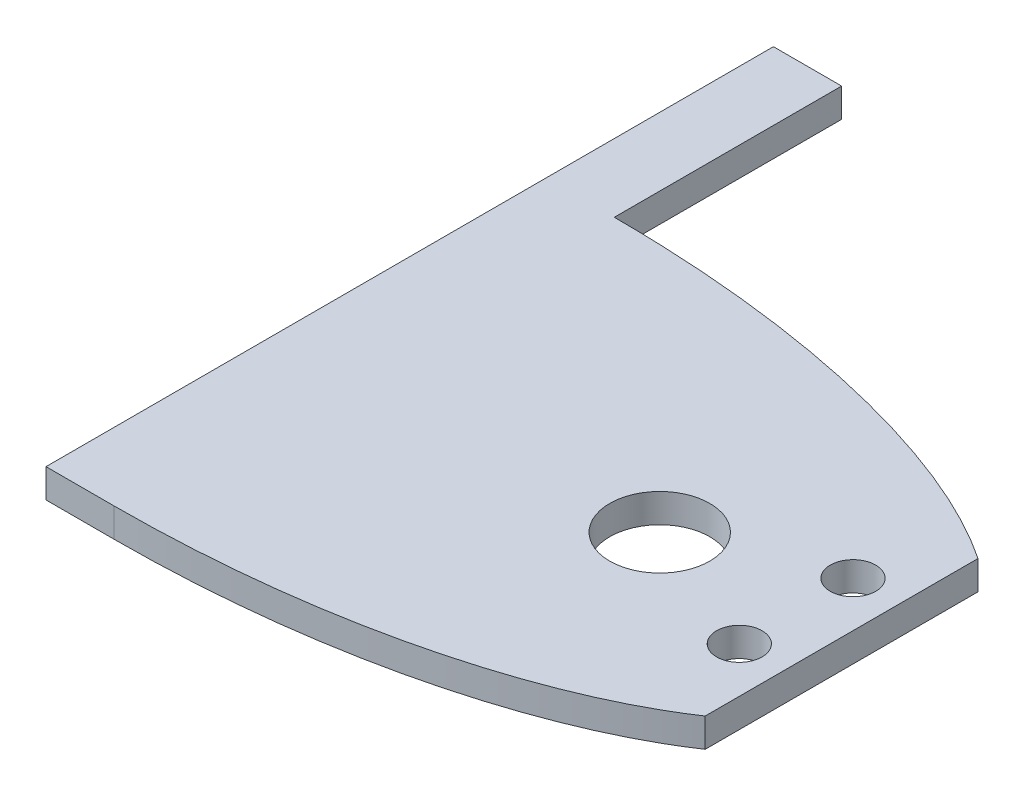
SolidWorks part; units mm, degrees
ref_plane "Front Plane" through (0, 0, 0) normal (0, 0, 1) x (1, 0, 0)
ref_plane "Top Plane" through (0, 0, 0) normal (0, 1, 0) x (1, 0, 0)
ref_plane "Right Plane" through (0, 0, 0) normal (1, 0, 0) x (0, 0, -1)
sketch "Sketch1" plane through (0, 0, 0) normal (0, 1, 0) x (1, 0, 0)
  line L1 (0, 110) -> (0, 0)
  line L2 (105, 85) -> (105, 25)
  ellipse E0 centre (0, 55) end of major axis (-125.2773, 55) minor radius 55 (105, 85) -> (0, 110) ccw
  ellipse E1 centre (0, 55) end of major axis (-125.2773, 55) minor radius 55 (0, 0) -> (105, 25) ccw
  dimension "D1" = 110
  dimension "D2" = 60
  dimension "D3" = 105
extrude "Boss-Extrude1" add sketch "Sketch1" along normal blind 6.35
sketch "Sketch2" plane through (0, 0, 0) normal (0, 1, 0) x (1, 0, 0)
  circle A0 centre (95, 67.5) radius 5
  circle A1 centre (95, 42.5) radius 5
  dimension "D1" = 10
  dimension "D4" = 10
  dimension "D2" = 17.5
  dimension "D3" = 42.5
extrude "Cut-Extrude1" cut sketch "Sketch2" along normal blind 6.35
sketch "Sketch3" plane through (0, 0, 0) normal (0, 1, 0) x (1, 0, 0)
  circle A0 centre (65, 55) radius 11
  dimension "D2" = 22
  dimension "D1" = 30
  dimension "D3" = 40
extrude "Cut-Extrude2" cut sketch "Sketch3" along normal through all
sketch "Sketch4" plane through (0, 0, 0) normal (0, 1, 0) x (1, 0, 0)
  line L0 (0, 110) -> (-15, 110)
  line L1 (0, 110) -> (0, 0) construction
  line L2 (-15, 110) -> (-15, 0)
  line L3 (-15, 0) -> (0, 0)
  line L4 (0, 0) -> (0, 110)
  ellipse E0 centre (0, 55) end of major axis (-125.2773, 55) minor radius 55 (105, 85) -> (0, 110) ccw construction
  dimension "D1" = 15
extrude "Boss-Extrude3" add sketch "Sketch4" along normal blind 6.35
sketch "Sketch5" plane through (0, 0, 0) normal (0, 1, 0) x (1, 0, 0)
  line L0 (-15, 110) -> (-15, 160)
  line L1 (-15, 160) -> (0, 160)
  line L2 (0, 160) -> (0, 110)
  line L3 (0, 110) -> (-15, 110)
  dimension "D1" = 50
extrude "Boss-Extrude4" add sketch "Sketch5" along normal blind 6.35
